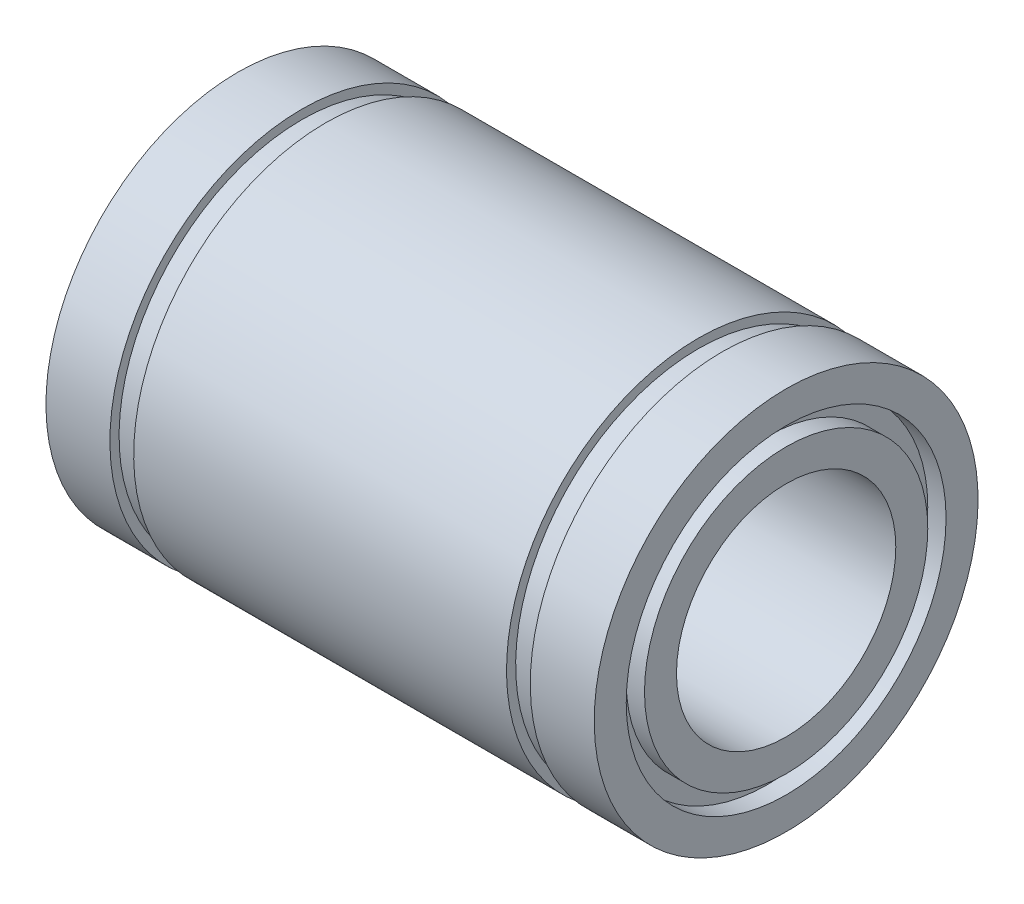
SolidWorks part; units mm, degrees
material "Ст3сп ГОСТ 535-2005"
ref_plane "Plano frontal" through (0, 0, 0) normal (0, 0, 1) x (1, 0, 0)
ref_plane "Plano superior" through (0, 0, 0) normal (0, 1, 0) x (1, 0, 0)
ref_plane "Plano direito" through (0, 0, 0) normal (1, 0, 0) x (0, 0, -1)
sketch "Esboço1" plane through (0, 0, 0) normal (0, 0, 1) x (1, 0, 0)
  line L0 (-15, 10.5) -> (-11.5, 10.5)
  line L1 (-11.5, 10.5) -> (-11.5, 10)
  line L2 (-11.5, 10) -> (-10.2, 10)
  line L3 (-10.2, 10) -> (-10.2, 10.5)
  line L4 (-10.2, 10.5) -> (10.2, 10.5)
  line L5 (10.2, 10.5) -> (10.2, 10)
  line L6 (10.2, 10) -> (11.5, 10)
  line L7 (11.5, 10) -> (11.5, 10.5)
  line L8 (11.5, 10.5) -> (15, 10.5)
  line L9 (15, 10.5) -> (15, 8.75)
  line L10 (15, 6) -> (-15, 6)
  line L11 (-15, 6) -> (-15, 7.75)
  line L12 (0, 6) -> (0, 0) construction
  line L13 (0, 0) -> (-86.5, 0) construction
  line L14 (-15, 8.75) -> (-15, 10.5)
  line L15 (-15, 8.75) -> (-14, 8.75)
  line L16 (15, 7.75) -> (15, 6)
  line L17 (-14, 8.75) -> (-14, 7.75)
  line L18 (-14, 7.75) -> (-15, 7.75)
  line L19 (15, 8.75) -> (14, 8.75)
  line L21 (15, 7.75) -> (14, 7.75)
  line L22 (14, 8.75) -> (14, 7.75)
  dimension "D1" = 30
  dimension "D2" = 23
  dimension "D3" = 1.3
  dimension "D4" = 12
  dimension "D5" = 21
  dimension "D6" = 20
  dimension "D7" = 1
  dimension "D8" = 1
  dimension "D9" = 1
  dimension "D10" = 1
revolve "Revolução1" add sketch "Esboço1" angle 360 about L13
